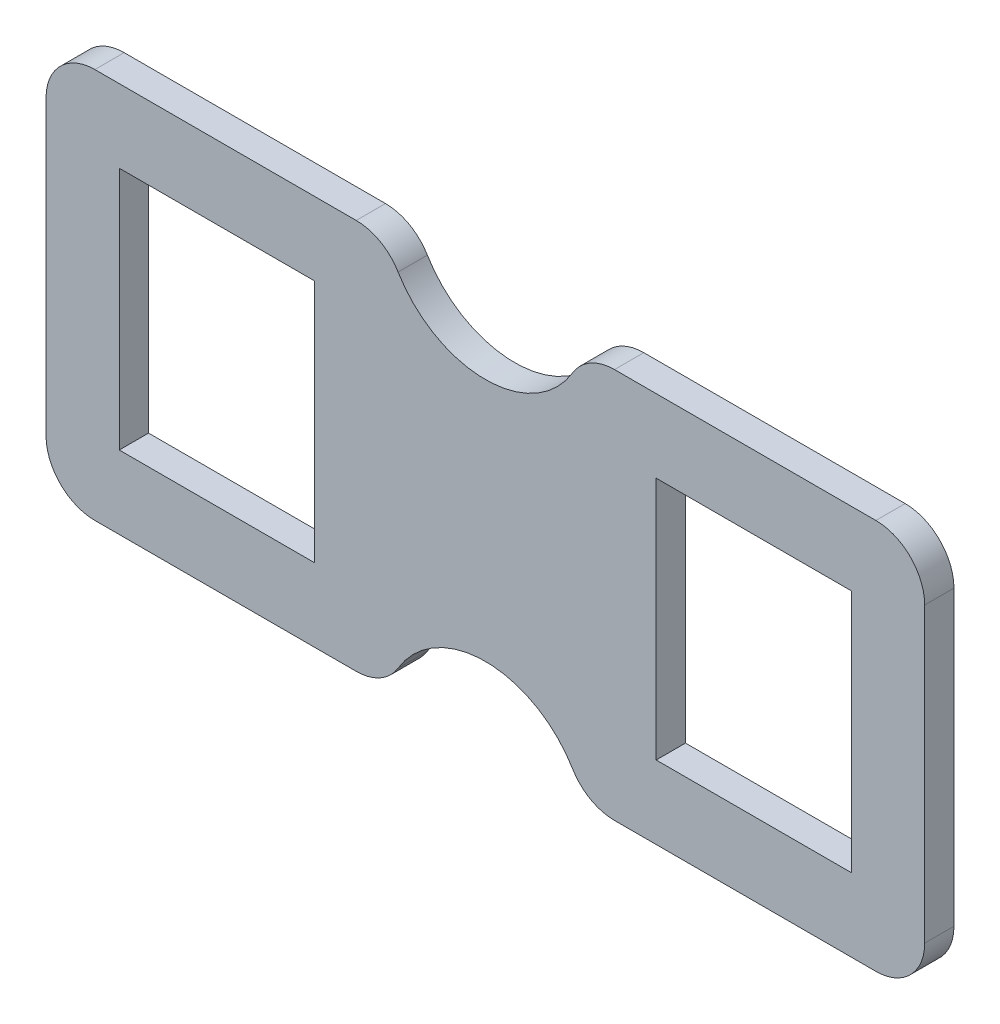
SolidWorks part; units mm, degrees
ref_plane "Front" through (0, 0, 0) normal (0, 0, 1) x (1, 0, 0)
ref_plane "Top" through (0, 0, 0) normal (0, 1, 0) x (1, 0, 0)
ref_plane "Right" through (0, 0, 0) normal (1, 0, 0) x (0, 0, -1)
sketch "Sketch1" plane through (0, 0, 0) normal (0, 0, 1) x (1, 0, 0)
  line L0 (-228.6, 82.55) -> (0, 82.55) construction
  line L1 (0, 0) -> (-88.9, 0)
  line L2 (0, 0) -> (0, 101.6)
  line L3 (0, 101.6) -> (-88.9, 101.6)
  line L4 (-228.6, 0) -> (-228.6, 101.6)
  line L5 (-209.55, 82.55) -> (-158.75, 82.55)
  line L6 (-209.55, 82.55) -> (-209.55, 19.05)
  line L7 (-209.55, 19.05) -> (-158.75, 19.05)
  line L8 (-158.75, 82.55) -> (-158.75, 19.05)
  line L9 (-69.85, 19.05) -> (-19.05, 19.05)
  line L10 (-69.85, 19.05) -> (-69.85, 82.55)
  line L11 (-69.85, 82.55) -> (-19.05, 82.55)
  line L12 (-19.05, 19.05) -> (-19.05, 82.55)
  line L14 (-139.7, 101.6) -> (-139.7, 82.55) construction
  line L15 (-139.7, 82.55) -> (-88.9, 82.55) construction
  line L16 (-88.9, 101.6) -> (-88.9, 82.55) construction
  line L21 (-139.7, 101.6) -> (-228.6, 101.6)
  line L22 (-228.6, 50.8) -> (0, 50.8) construction
  line L23 (-139.7, 0) -> (-228.6, 0)
  arc A0 (-139.7, 101.6) -> (-88.9, 101.6) centre (-114.3, 109.0083) ccw
  arc A1 (-139.7, 0) -> (-88.9, 0) centre (-114.3, -7.4083) cw
  point P23 (-114.3, 82.55)
  point P24 (-114.3, 82.55)
  dimension "D1" = 101.6
  dimension "D2" = 228.6
  dimension "D3" = 19.05
  dimension "D4" = 50.8
  dimension "D5" = 19.05
  dimension "D6" = 19.05
  dimension "D7" = 19.05
  dimension "D8" = 19.05
  dimension "D9" = 50.8
extrude "Boss-Extrude1" add sketch "Sketch1" along normal blind 7.62
fillet "Fillet1" radius 12.7 8 edges at (-228.6, 101.6, 3.81) (-228.6, 0, 3.81) (-139.7, 0, 3.81) (-88.9, 0, 3.81) (0, 0, 3.81) (0, 101.6, 3.81) (-88.9, 101.6, 3.81) (-139.7, 101.6, 3.81)
equation "\"D8@Sketch1\"=\"D7@Sketch1\""
